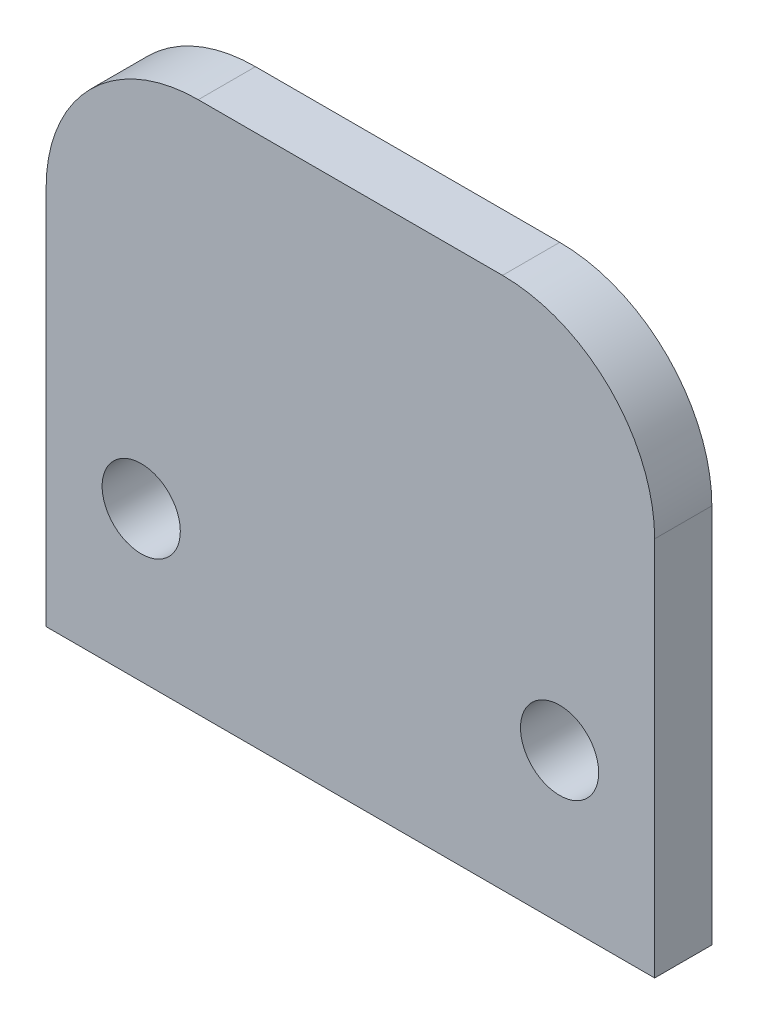
SolidWorks part; units mm, degrees
material "6061 Alloy"
ref_plane "Front Plane" through (0, 0, 0) normal (0, 0, 1) x (1, 0, 0)
ref_plane "Top Plane" through (0, 0, 0) normal (0, 1, 0) x (1, 0, 0)
ref_plane "Right Plane" through (0, 0, 0) normal (1, 0, 0) x (0, 0, -1)
sketch "Sketch1" plane through (0, 0, 0) normal (0, 0, 1) x (1, 0, 0)
  line L1 (-25.4, 0) -> (25.4, 0)
  line L2 (-25.4, 0) -> (-25.4, 44.45)
  line L4 (25.4, 0) -> (25.4, 44.45)
  line L5 (-25.4, 44.45) -> (25.4, 44.45)
  point P2 (25.4, 43.5411)
  point P4 (0, 0)
  point P5 (-25.4, 43.1902)
  dimension "D1" = 50.8
  dimension "D2" = 44.45
extrude "Boss-Extrude1" add sketch "Sketch1" along normal mid plane 4.7752
hole_wizard "F (0.257) Diameter Hole1" positions "Sketch2" profile "Sketch3" hole size "F" standard "ANSI Inch" end condition through all
sketch "Sketch2" plane through (0, 0, 2.3876) normal (0, 0, 1) x (1, 0, 0)
  line L0 (-25.4, 0) -> (25.4, 0) construction
  line L1 (-17.4625, 12.4968) -> (17.4625, 12.4968) construction
  point P0 (-17.4625, 12.4968)
  point P2 (17.4625, 12.4968)
  point P14 (0, 12.4968)
  dimension "D1" = 34.925
  dimension "D2" = 12.4968
sketch "Sketch3" plane through (-17.4625, 12.4968, 2.3876) normal (1, 0, 0) x (0, -1, 0)
  line L0 (0, 0) -> (0, 4.7752)
  line L1 (0, 4.7752) -> (3.2639, 4.7752)
  line L2 (3.2639, 4.7752) -> (3.2639, 0)
  line L5 (3.2639, 0) -> (0, 0)
  line L11 (0, -6.35) -> (0, 107.95) construction
  dimension "Thru Hole Dia." = 6.5278
  dimension "Thru Hole Depth" = 4.7752
fillet "Fillet1" radius 12.7 2 edges at (25.4, 44.45, 0) (-25.4, 44.45, 0)
